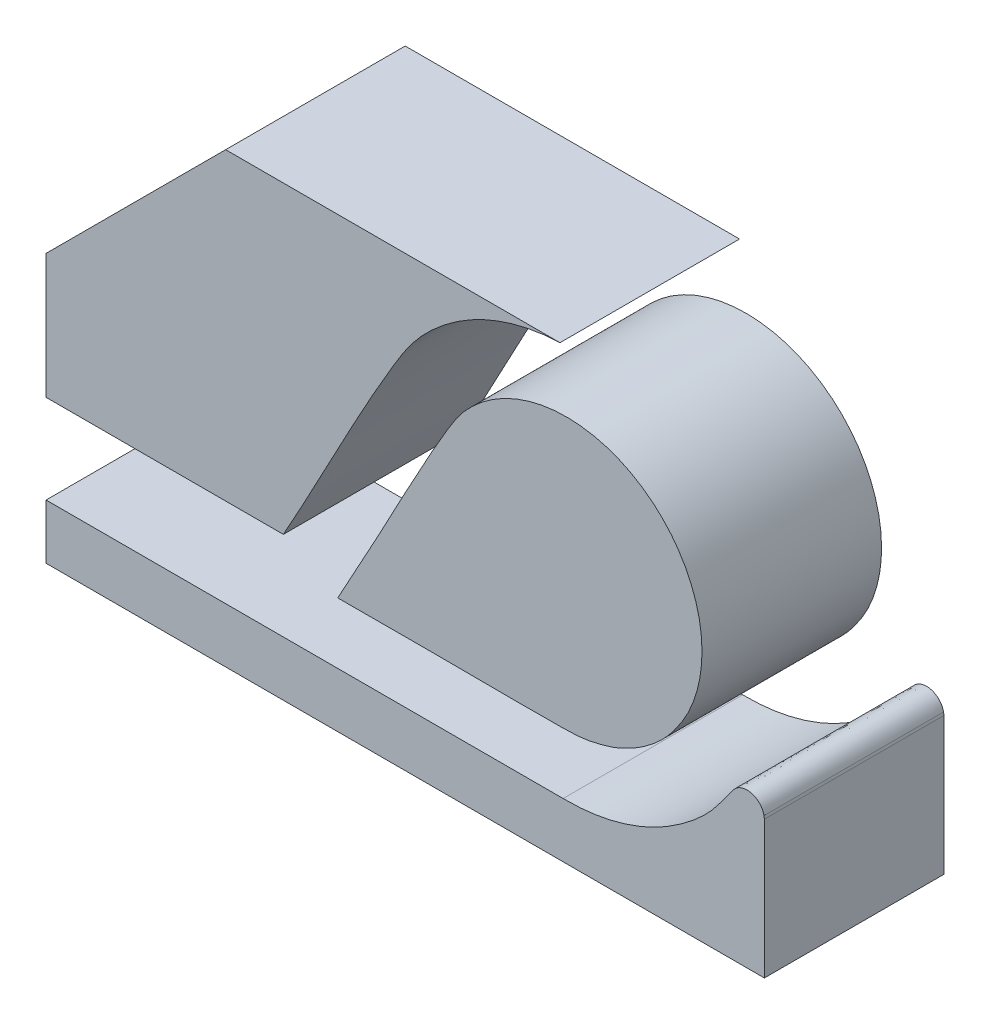
SolidWorks part; units mm, degrees
ref_plane "Front Plane" through (0, 0, 0) normal (0, 0, 1) x (1, 0, 0)
ref_plane "Top Plane" through (0, 0, 0) normal (0, 1, 0) x (1, 0, 0)
ref_plane "Right Plane" through (0, 0, 0) normal (1, 0, 0) x (0, 0, -1)
sketch "Sketch1" plane through (0, 0, 0) normal (0, 0, 1) x (1, 0, 0)
  line L0 (-81.5162, 20.6579) -> (-81.5162, 17.1854)
  line L1 (-81.5162, 17.1854) -> (-74.9087, 17.1854)
  line L2 (-73.395, 16.4104) -> (-73.1638, 16.4104)
  line L3 (-67.207, 25.6579) -> (-76.5162, 25.6579)
  line L4 (-76.5162, 25.6579) -> (-81.5162, 20.6579)
  line L5 (-81.5162, 13.1843) -> (-61.5162, 13.1843)
  line L6 (-81.5162, 14.7104) -> (-81.5162, 13.1843)
  line L7 (-61.5262, 17.0949) -> (-61.5162, 17.0158)
  line L15 (-61.5162, 17.0158) -> (-61.5162, 13.1843)
  line L45 (-61.5162, 13.1843) -> (-61.5162, 17.0158)
  line L72 (-74.9087, 17.1854) -> (-81.5162, 17.1854)
  line L74 (-81.5162, 14.7104) -> (-67.0412, 14.7104)
  spline S0 degree 3 poles (-67.207, 25.6579) (-67.8413, 25.6377) (-68.786, 25.4384) (-69.9236, 24.865) (-70.6872, 24.2927) (-71.3494, 23.6016) (-72.7993, 21.2411) (-73.8673, 19.0427) (-74.9087, 17.1854) knots 0 0 0 0 0.157243 0.235864 0.314486 0.393107 0.471729 1 1 1 1
  spline S1 degree 3 poles (-73.395, 16.4104) (-73.0277, 17.0757) (-72.0066, 18.9259) (-70.9491, 20.9952) (-70.0234, 22.5186) (-69.5842, 22.9858) (-69.0781, 23.3766) (-68.5121, 23.6757) (-67.9043, 23.8757) (-67.2714, 23.9705) (-66.6316, 23.9576) (-66.003, 23.8373) (-65.4036, 23.6131) (-64.8505, 23.2913) (-64.3593, 22.8811) (-63.9441, 22.3941) (-63.6166, 21.8443) (-63.3863, 21.2472) (-63.2596, 20.6199) (-63.2403, 19.9803) (-63.3282, 19.3462) (-63.4963, 18.8229) (-63.6556, 18.477) (-63.8702, 18.1107) (-64.1659, 17.6858) (-64.5889, 17.2905) (-64.9323, 17.0399) (-65.2051, 16.8741) (-65.4912, 16.7331) (-65.7376, 16.6324) (-65.9926, 16.5579) (-66.1984, 16.5054) (-66.4579, 16.4488) (-66.7224, 16.4178) (-67.7359, 16.3926) (-69.7397, 16.4213) (-71.7806, 16.4101) (-73.0204, 16.4103) (-73.1638, 16.4104) knots 0 0 0 0 0.080305 0.223311 0.245749 0.268186 0.290624 0.313061 0.335499 0.357936 0.380374 0.402811 0.425249 0.447686 0.470124 0.492561 0.514999 0.537436 0.559874 0.582311 0.604749 0.627186 0.640158 0.644901 0.672053 0.69449 0.705719 0.716948 0.728177 0.739405 0.74502 0.756239 0.761853 0.773082 0.78431 0.868972 0.984844 1 1 1 1
  spline S2 degree 3 poles (-67.1198, 14.7104) (-67.0936, 14.7102) (-66.7571, 14.7102) (-66.118, 14.7589) (-65.2199, 14.9904) (-64.5108, 15.304) (-63.9917, 15.625) (-63.4872, 15.9881) (-62.9165, 16.5101) (-62.565, 17.0505) (-62.3423, 17.3353) (-62.281, 17.3871) (-62.2126, 17.4287) (-62.1381, 17.4582) (-62.0598, 17.4751) (-61.9798, 17.4788) (-61.9002, 17.4693) (-61.8233, 17.4467) (-61.7512, 17.4118) (-61.6859, 17.3655) (-61.629, 17.3091) (-61.5825, 17.244) (-61.5465, 17.1722) (-61.5327, 17.1207) (-61.5262, 17.0949) knots 0.429056 0.429056 0.429056 0.429056 0.433439 0.485345 0.53725 0.589155 0.615108 0.64106 0.692965 0.744871 0.749357 0.753843 0.758329 0.762815 0.767301 0.771787 0.776273 0.780759 0.785245 0.789732 0.794218 0.798704 0.80319 0.807676 0.807676 0.807676 0.807676
extrude "Boss-Extrude1" add sketch "Sketch1" along normal blind 5
